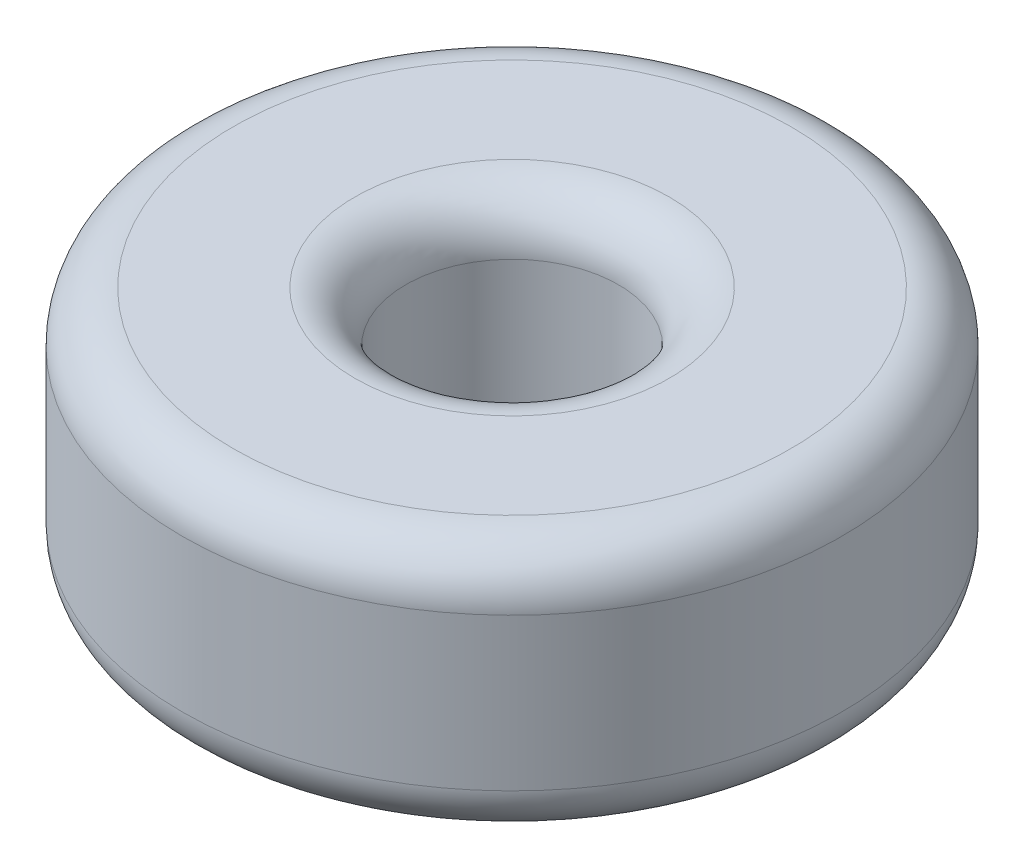
SolidWorks part; units mm, degrees
ref_plane "Front Plane" through (0, 0, 0) normal (0, 0, 1) x (1, 0, 0)
ref_plane "Top Plane" through (0, 0, 0) normal (0, 1, 0) x (1, 0, 0)
ref_plane "Right Plane" through (0, 0, 0) normal (1, 0, 0) x (0, 0, -1)
sketch "Sketch1" plane through (0, 0, 0) normal (0, 1, 0) x (1, 0, 0)
  circle A0 centre (0, 0) radius 6.5
  circle A1 centre (0, 0) radius 2.1
  dimension "D1" = 4.2
  dimension "D2" = 13
extrude "Boss-Extrude1" add sketch "Sketch1" along normal blind 5
fillet "Fillet1" radius 1 4 edges at (0, 0, 2.1) (0, 0, 6.5) (0, 5, 2.1) (0, 5, 6.5)
